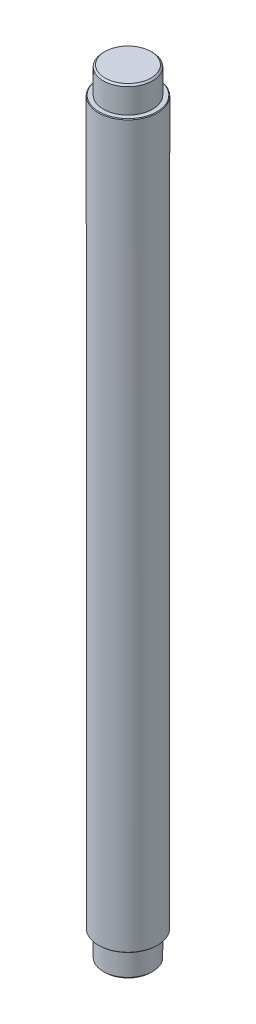
SolidWorks part; units mm, degrees
material "Q235-A"
ref_plane "前视基准面" through (0, 0, 0) normal (0, 0, 1) x (1, 0, 0)
ref_plane "上视基准面" through (0, 0, 0) normal (0, 1, 0) x (1, 0, 0)
ref_plane "右视基准面" through (0, 0, 0) normal (1, 0, 0) x (0, 0, -1)
sketch "草图1" plane through (0, 0, 0) normal (0, 0, 1) x (1, 0, 0)
  line L0 (0, 0) -> (0, 118) construction
  line L1 (0, 0) -> (66.9609, 0) construction
  line L2 (0, 118) -> (0, -118)
  line L3 (0, -118) -> (-7.5, -118)
  line L4 (-7.5, -118) -> (-7.5, -110)
  line L5 (-7.5, -110) -> (-9, -110)
  line L6 (-9, -110) -> (-9, 110)
  line L7 (-9, 110) -> (-7.5, 110)
  line L8 (-7.5, 110) -> (-7.5, 118)
  line L9 (-7.5, 118) -> (0, 118)
  dimension "D1" = 220
  dimension "D2" = 236
  dimension "D3" = 18
  dimension "D4" = 7.5
revolve "旋转1" add sketch "草图1" angle 360 about L2
chamfer "倒角1" distance 0.5 angle 45 2 edges at (-7.5, -118, 0) (-7.5, 118, 0)
ref_plane "Plane1" through (0, 0, -9) normal (0, 0, 1) x (1, 0, 0)
hole_wizard "Ø6.0 (6) 直径孔4" positions "草图4" profile "草图3" hole size "Ø6.0" standard "GB"
sketch "草图4" plane through (0, 0, -9) normal (0, 0, 1) x (1, 0, 0)
  line L0 (0, 0) -> (0, 141.9953) construction
  point P0 (0, -32.5)
  point P2 (0, 32.5)
  point P4 (0, 80.5)
  point P6 (0, -80.5)
  dimension "D1" = 32.5
  dimension "D2" = 32.5
  dimension "D3" = 48
  dimension "D4" = 48
sketch "草图3" plane through (0, -32.5, -9) normal (1, 0, 0) x (0, 1, 0)
  line L0 (0, 0) -> (0, 3.8026)
  line L1 (0, 3.8026) -> (3, 2)
  line L2 (3, 2) -> (3, 0)
  line L5 (3, 0) -> (0, 0)
  line L10 (0, 3.8026) -> (-3, 2) construction
  line L11 (0, -6.35) -> (0, 107.95) construction
  dimension "孔直径" = 6
  dimension "孔深度" = 2
  dimension "导头角度" = 118
pattern_circular "阵列(圆周)1" count 4 over 360 about axis through (0, 118, 0) along (0, 1, 0) of "Ø6.0 (6) 直径孔4"
chamfer "倒角2" distance 0.2 angle 45 2 edges at (-9, -110, 0) (-9, 110, 0)
